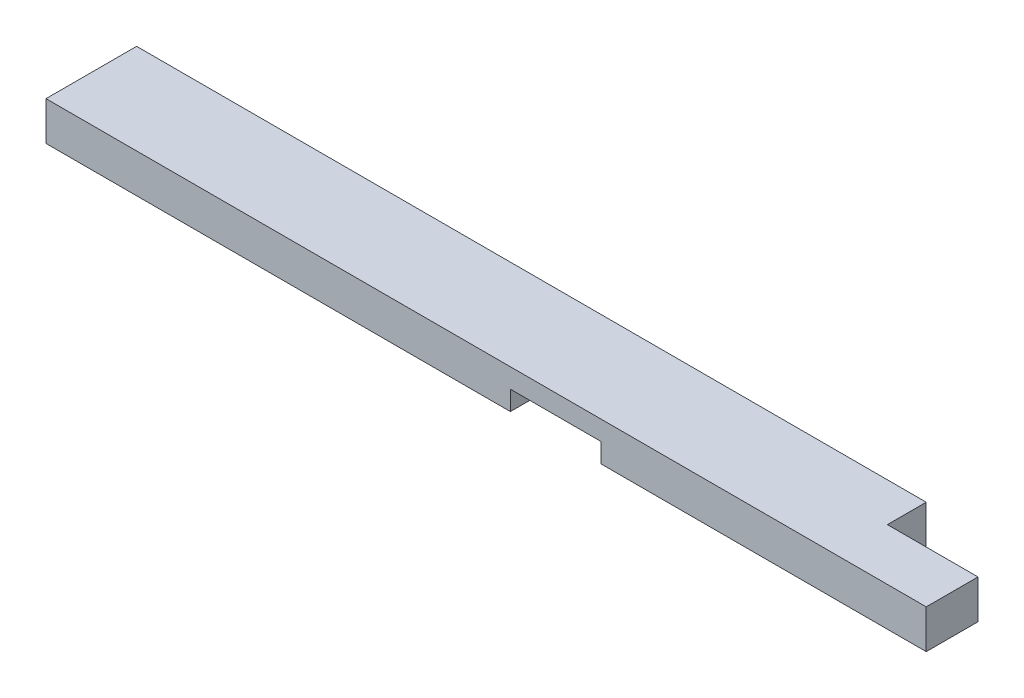
SolidWorks part; units mm, degrees
material "Pine"
ref_plane "Front Plane" through (0, 0, 0) normal (0, 0, 1) x (1, 0, 0)
ref_plane "Top Plane" through (0, 0, 0) normal (0, 1, 0) x (1, 0, 0)
ref_plane "Right Plane" through (0, 0, 0) normal (1, 0, 0) x (0, 0, -1)
sketch "Sketch1" plane through (0, 0, 0) normal (0, 1, 0) x (1, 0, 0)
  line L1 (0, 0) -> (863.6, 0)
  line L2 (0, 0) -> (0, 88.9)
  line L3 (0, 88.9) -> (863.6, 88.9)
  line L4 (863.6, 0) -> (863.6, 88.9)
  dimension "D1" = 88.9
  dimension "D2" = 863.6
extrude "Boss-Extrude1" add sketch "Sketch1" along normal blind 38.1
sketch "Sketch3" plane through (0, 38.1, 0) normal (0, 1, 0) x (1, 0, 0)
  line L1 (863.6, 88.9) -> (774.7, 88.9)
  line L2 (863.6, 88.9) -> (863.6, 50.8)
  line L3 (863.6, 50.8) -> (774.7, 50.8)
  line L4 (774.7, 88.9) -> (774.7, 50.8)
  dimension "D1" = 774.7
  dimension "D2" = 38.1
extrude "Cut-Extrude2" cut sketch "Sketch3" against normal through all
sketch "Sketch4" plane through (0, 0, -88.9) normal (0, 0, -1) x (-1, 0, 0)
  line L1 (-544.5125, 19.05) -> (-455.6125, 19.05)
  line L2 (-544.5125, 19.05) -> (-544.5125, 0)
  line L3 (-544.5125, 0) -> (-455.6125, 0)
  line L5 (-774.7, 0) -> (0, 0) construction
  line L6 (-455.6125, 19.05) -> (-455.6125, 0)
  dimension "D1" = 19.05
  dimension "D2" = 455.6125
  dimension "D3" = 88.9
extrude "Cut-Extrude3" cut sketch "Sketch4" against normal through all
